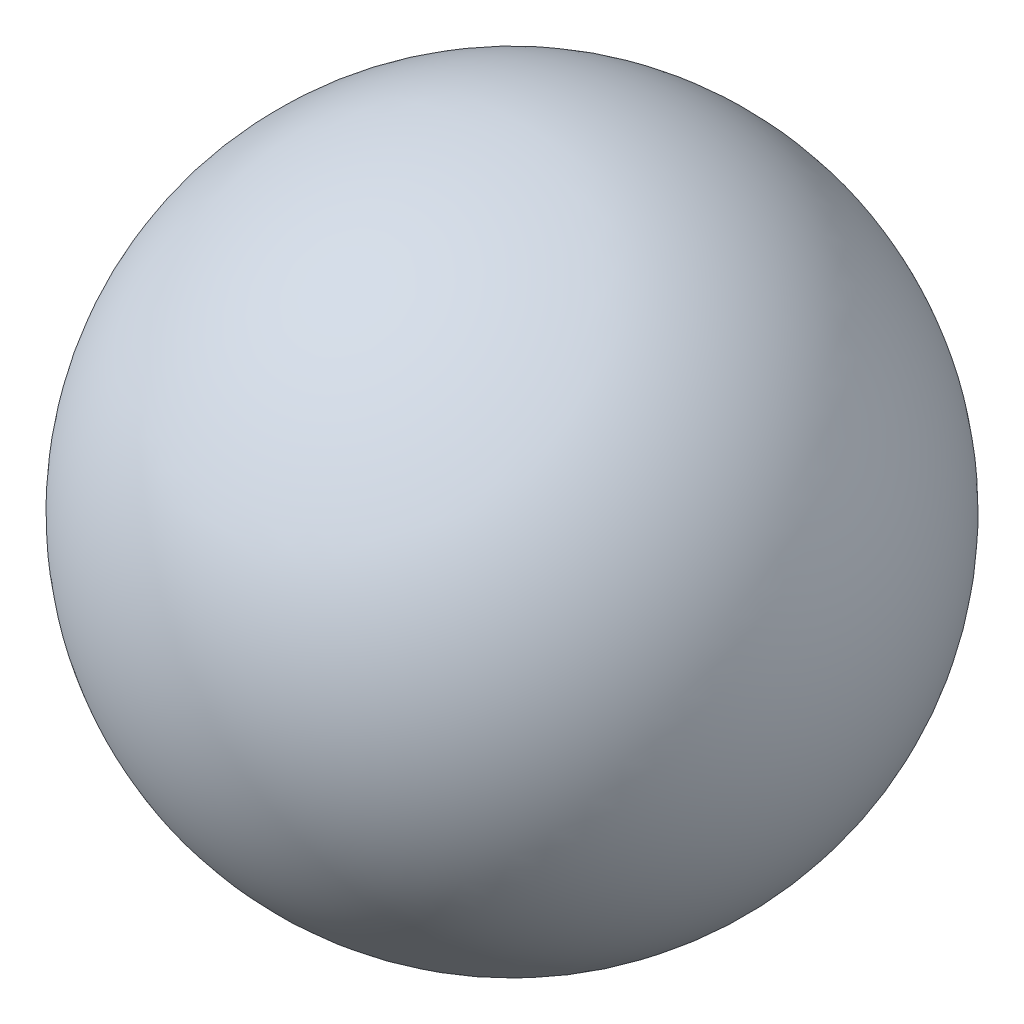
SolidWorks part; units mm, degrees
ref_plane "Front Plane" through (0, 0, 0) normal (0, 0, 1) x (1, 0, 0)
ref_plane "Top Plane" through (0, 0, 0) normal (0, 1, 0) x (1, 0, 0)
ref_plane "Right Plane" through (0, 0, 0) normal (1, 0, 0) x (0, 0, -1)
sketch "Sketch1" plane through (0, 0, 0) normal (0, 1, 0) x (1, 0, 0)
  line L0 (1.5, 1.81) -> (1.5, -1.19)
  line L1 (1.5, 1.81) -> (1.5, -1.19) construction
  arc A0 (1.5, -1.19) -> (1.5, 1.81) centre (1.5, 0.31) ccw
  dimension "D1" = 1.5
revolve "Revolve1" add sketch "Sketch1" angle 360 about L1
